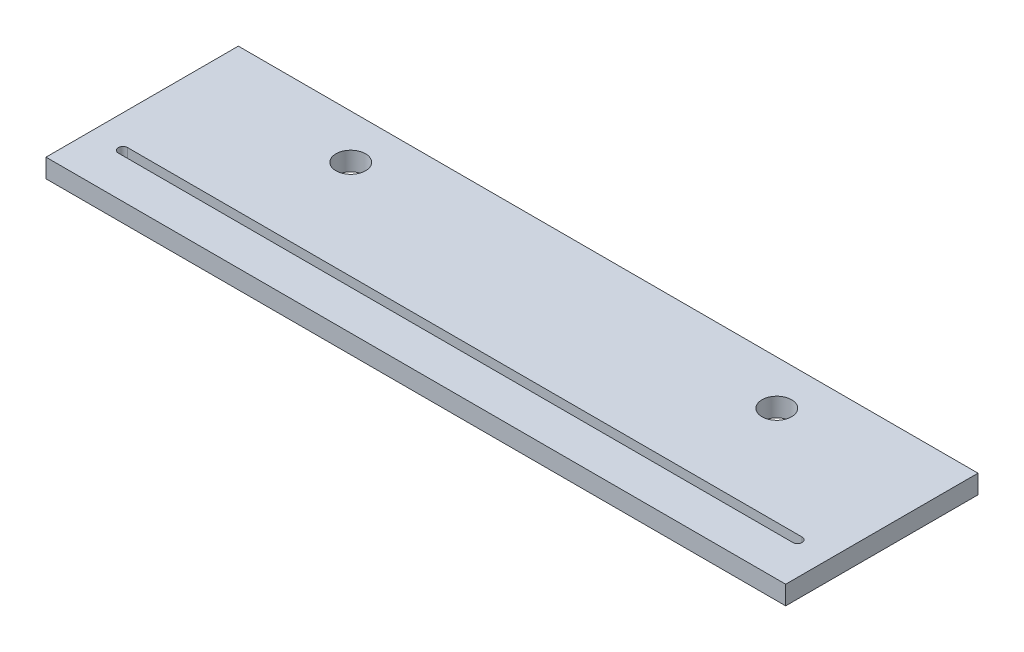
SolidWorks part; units mm, degrees
ref_plane "Alzado" through (0, 0, 0) normal (0, 0, 1) x (1, 0, 0)
ref_plane "Planta" through (0, 0, 0) normal (0, 1, 0) x (1, 0, 0)
ref_plane "Vista lateral" through (0, 0, 0) normal (1, 0, 0) x (0, 0, -1)
sketch "Croquis1" plane through (0, 0, 0) normal (0, 1, 0) x (1, 0, 0)
  line L0 (-125, -25) -> (-125, -40)
  line L2 (-125, -25) -> (-125, 25)
  line L3 (-125, 25) -> (125, 25)
  line L4 (125, -25) -> (125, 25)
  line L5 (-125, -25) -> (125, 25) construction
  line L6 (-125, 25) -> (125, -25) construction
  line L7 (-125, -40) -> (125, -40)
  line L8 (125, -40) -> (125, -25)
  point P0 (0, 0)
  dimension "D1" = 250
  dimension "D3" = 65
extrude "Saliente-Extruir1" add sketch "Croquis1" along normal blind 6.35
sketch "Croquis2" plane through (0, 6.35, 0) normal (0, 1, 0) x (1, 0, 0)
  line L0 (125, 25) -> (-125, 25) construction
  line L1 (-125, 25) -> (-125, -40) construction
  line L2 (125, -40) -> (125, 25) construction
  line L3 (0, 25) -> (0, -40) construction
  line L4 (-125, -40) -> (125, -40) construction
  line L5 (114, -23.4125) -> (-114, -23.4125)
  line L6 (-114, -26.5875) -> (114, -26.5875)
  arc A1 (-114, -23.4125) -> (-114, -26.5875) centre (-114, -25) ccw
  arc A2 (114, -26.5875) -> (114, -23.4125) centre (114, -25) ccw
  circle A7 centre (-72, 10) radius 5
  circle A8 centre (72, 10) radius 5
  dimension "D7" = 10
  dimension "D8" = 10
  dimension "D2" = 11
  dimension "D3" = 72
  dimension "D4" = 72
  dimension "D5" = 11
  dimension "D11" = 15
  dimension "D12" = 15
extrude "Cortar-Extruir3" cut sketch "Croquis2" against normal through all
